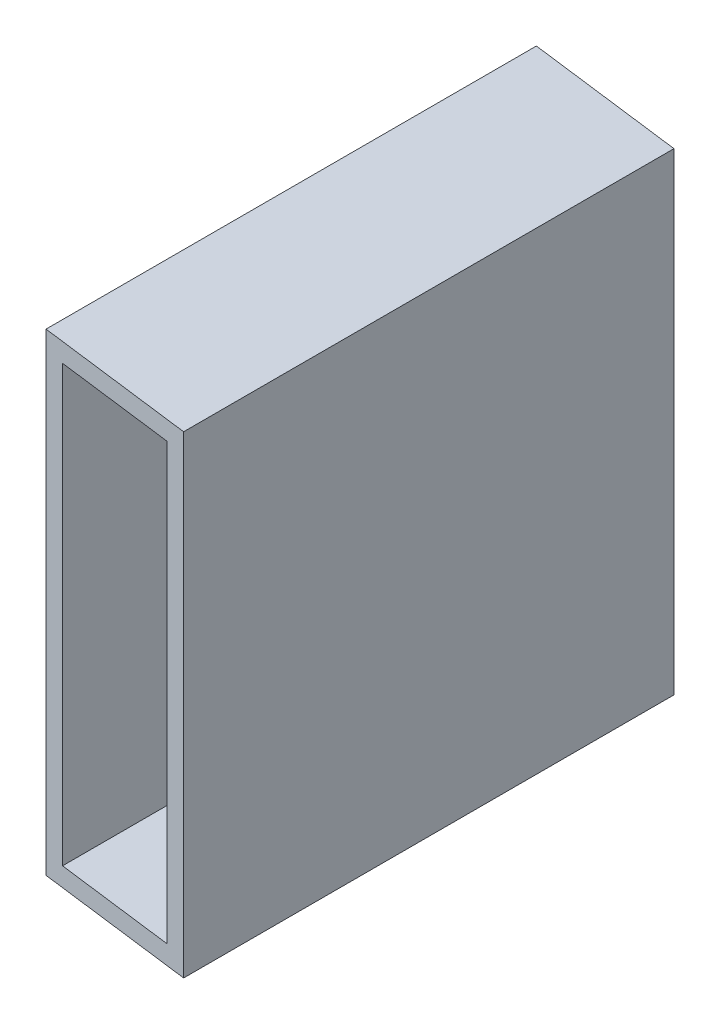
SolidWorks part; units mm, degrees
material "A500"
ref_plane "Front Plane" through (0, 0, 0) normal (0, 0, 1) x (1, 0, 0)
ref_plane "Top Plane" through (0, 0, 0) normal (0, 1, 0) x (1, 0, 0)
ref_plane "Right Plane" through (0, 0, 0) normal (1, 0, 0) x (0, 0, -1)
sketch "Sketch2" plane through (0, 0, 0) normal (0, 0, 1) x (1, 0, 0)
  line L0 (0, 0) -> (0, 38.1)
  line L1 (0, 38.1) -> (12.7, 38.1)
  line L2 (12.7, 38.1) -> (12.7, 0)
  line L3 (12.7, 0) -> (0, 0)
  line L4 (12.7, -38.1) -> (12.7, -35.052)
  line L5 (0, 0) -> (-12.7, 0)
  line L6 (0, 0) -> (0, -38.1)
  line L7 (0, -38.1) -> (-12.7, -38.1)
  line L8 (-12.7, 0) -> (-12.7, -38.1)
  line L9 (-12.7, -38.1) -> (12.7, -38.1)
  line L10 (-12.7, -38.1) -> (-12.7, 38.1)
  line L11 (-12.7, 38.1) -> (12.7, 38.1)
  line L12 (12.7, -38.1) -> (12.7, 38.1)
  line L13 (12.7, -35.052) -> (9.652, -35.052)
  line L14 (-12.7, 38.1) -> (-9.652, 38.1)
  line L15 (-9.652, 38.1) -> (-9.652, 35.052)
  line L17 (-9.652, 35.052) -> (9.652, 35.052)
  line L18 (-9.652, 35.052) -> (-9.652, -35.052)
  line L19 (-9.652, -35.052) -> (9.652, -35.052)
  line L20 (9.652, 35.052) -> (9.652, -35.052)
  dimension "D1" = 38.1
  dimension "D2" = 12.7
  dimension "D3" = 38.1
  dimension "D4" = 12.7
  dimension "D5" = 3.048
  dimension "D6" = 3.048
  dimension "D7" = 3.048
  dimension "D8" = 3.048
extrude "Boss-Extrude1" add sketch "Sketch2" along normal up to vertex (78.9851 mm away) contours L18 L15 L11 L10 L5 | L15 L17 L0 L11 | L17 L20 L3 L2 L1 L0 | L3 L20 L13 L12 | L19 L18 L5 L8 L7 L6 | L19 L6 L9 L4 L13
sketch "Sketch3" plane through (0, 0, 0) normal (0, 0, -1) x (-1, 0, 0)
  line L1 (12.7, -38.1) -> (-12.7, -38.1)
  line L2 (12.7, -38.1) -> (12.7, 38.1)
  line L3 (12.7, 38.1) -> (-12.7, 38.1)
  line L4 (-12.7, -38.1) -> (-12.7, 38.1)
  line L5 (-9.652, 35.052) -> (9.652, 35.052)
  line L6 (-9.652, 35.052) -> (-9.652, -35.052)
  line L7 (-9.652, -35.052) -> (9.652, -35.052)
  line L8 (9.652, 35.052) -> (9.652, -35.052)
sketch "Sketch5" plane through (0, 0, 0) normal (0, 0, -1) x (-1, 0, 0)
  line L1 (12.7, -38.1) -> (-12.7, -38.1)
  line L2 (12.7, -38.1) -> (12.7, 38.1)
  line L3 (12.7, 38.1) -> (-12.7, 38.1)
  line L4 (-12.7, -38.1) -> (-12.7, 38.1)
  line L5 (-9.652, 35.052) -> (9.652, 35.052)
  line L6 (-9.652, 35.052) -> (-9.652, -35.052)
  line L7 (-9.652, -35.052) -> (9.652, -35.052)
  line L8 (9.652, 35.052) -> (9.652, -35.052)
extrude "Boss-Extrude3" add sketch "Sketch5" along normal blind 50
sketch "Sketch6" plane through (0, -38.1, 0) normal (0, -1, 0) x (1, 0, 0)
  line L0 (-45.2283, -5.7609) -> (38.1687, 4.8617)
  line L1 (12.534, -48.4035) -> (0, 0)
  line L2 (85.9833, -332.048) -> (0, 0) construction
  line L3 (0, 50) -> (0, 0)
  line L4 (0, 0) -> (0, 78.9851) construction
  line L5 (12.534, -48.4035) -> (38.1687, 4.8617)
  line L6 (0, 50) -> (38.1687, 4.8617)
  line L7 (38.1687, 4.8617) -> (-45.2283, -5.7609)
  line L8 (38.1687, 4.8617) -> (45.6403, -53.7974)
  line L9 (-45.2283, -5.7609) -> (-37.7566, -64.42)
  line L10 (45.6403, -53.7974) -> (-37.7566, -64.42)
  line M10 (-12.7, 78.9851) -> (-12.7, -50)
  line M11 (-12.7, -50) -> (12.7, -50)
  line M12 (12.7, -50) -> (12.7, 78.9851)
  dimension "D1" = 50
  dimension "D2" = 50
extrude "Cut-Extrude1" cut sketch "Sketch6" against normal through all both and the other way through all contours L10 L8 L5 L0 L9 M12 M11 M10 | L5 L1 L0 M10 M11 M12 | L5 L0 M12 | L1 L5 L0 M12
sketch "Sketch7" plane through (0, 0, 78.9851) normal (0, 0, 1) x (1, 0, 0)
  line L1 (12.7, -38.1) -> (-12.7, -38.1)
  line L2 (12.7, -38.1) -> (12.7, 38.1)
  line L3 (12.7, 38.1) -> (-12.7, 38.1)
  line L4 (-12.7, -38.1) -> (-12.7, 38.1)
  line L5 (-9.652, 35.052) -> (9.652, 35.052)
  line L6 (-9.652, 35.052) -> (-9.652, -35.052)
  line L7 (-9.652, -35.052) -> (9.652, -35.052)
  line L8 (9.652, 35.052) -> (9.652, -35.052)
extrude "Boss-Extrude4" add sketch "Sketch7" along normal blind 50
sketch "Sketch8" plane through (0, 38.1, 0) normal (0, 1, 0) x (1, 0, 0)
  line L0 (-24.3966, -75.8776) -> (24.3966, -82.0926)
  line L1 (0, -28.9851) -> (0, -78.9851)
  line L2 (0, 0) -> (0, -78.9851) construction
  line L3 (-12.534, -127.3886) -> (0, -78.9851)
  line L4 (-78.9642, -383.9272) -> (0, -78.9851) construction
  line L5 (-12.534, -127.3886) -> (-24.3966, -75.8776)
  line L6 (-24.3966, -75.8776) -> (0, -28.9851)
  line L11 (-24.3966, -75.8776) -> (-32.1542, -136.782)
  line L12 (24.3966, -82.0926) -> (16.639, -142.997)
  line L13 (-32.1542, -136.782) -> (16.639, -142.997)
  point P1 (0, -78.9851)
  dimension "D1" = 50
  dimension "D2" = 50
extrude "Cut-Extrude2" cut sketch "Sketch8" against normal through all both and the other way through all
equation "\"D3@Sketch2\"=\"D1@Sketch2\""
equation "\"D4@Sketch2\"=\"D2@Sketch2\""
